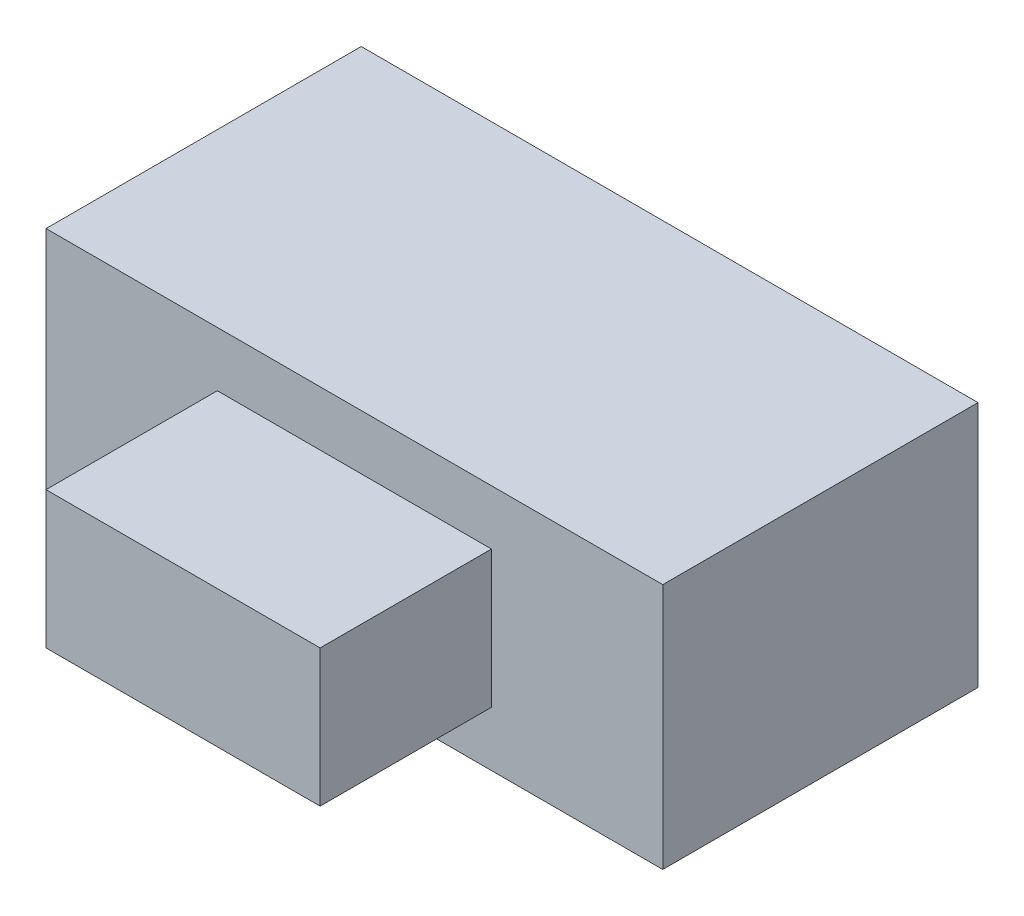
SolidWorks part; units mm, degrees
ref_plane "Front Plane" through (0, 0, 0) normal (0, 0, 1) x (1, 0, 0)
ref_plane "Top Plane" through (0, 0, 0) normal (0, 1, 0) x (1, 0, 0)
ref_plane "Right Plane" through (0, 0, 0) normal (1, 0, 0) x (0, 0, -1)
sketch "Sketch1" plane through (0, 0, 0) normal (0, 1, 0) x (1, 0, 0)
  line L1 (2.25, 1.15) -> (-2.25, 1.15)
  line L2 (2.25, 1.15) -> (2.25, -1.15)
  line L3 (2.25, -1.15) -> (-2.25, -1.15)
  line L4 (-2.25, 1.15) -> (-2.25, -1.15)
  line L5 (2.25, 1.15) -> (-2.25, -1.15) construction
  line L6 (2.25, -1.15) -> (-2.25, 1.15) construction
  point P0 (0, 0)
  dimension "D1" = 2.3
  dimension "D2" = 4.5
extrude "Boss-Extrude1" add sketch "Sketch1" along normal blind 1.8
sketch "Sketch2" plane through (0, 0, 1.15) normal (0, 0, 1) x (1, 0, 0)
  line L0 (0, 0) -> (0, 1.8) construction
  line L1 (1, 0.4) -> (-1, 0.4)
  line L2 (1, 0.4) -> (1, 1.4)
  line L3 (1, 1.4) -> (-1, 1.4)
  line L4 (-1, 0.4) -> (-1, 1.4)
  line L5 (1, 0.4) -> (-1, 1.4) construction
  line L6 (1, 1.4) -> (-1, 0.4) construction
  line L7 (-2.25, 1.8) -> (2.25, 1.8) construction
  point P0 (0, 0.9)
  dimension "D1" = 2
  dimension "D2" = 1
extrude "Boss-Extrude2" add sketch "Sketch2" along normal blind 1.25
